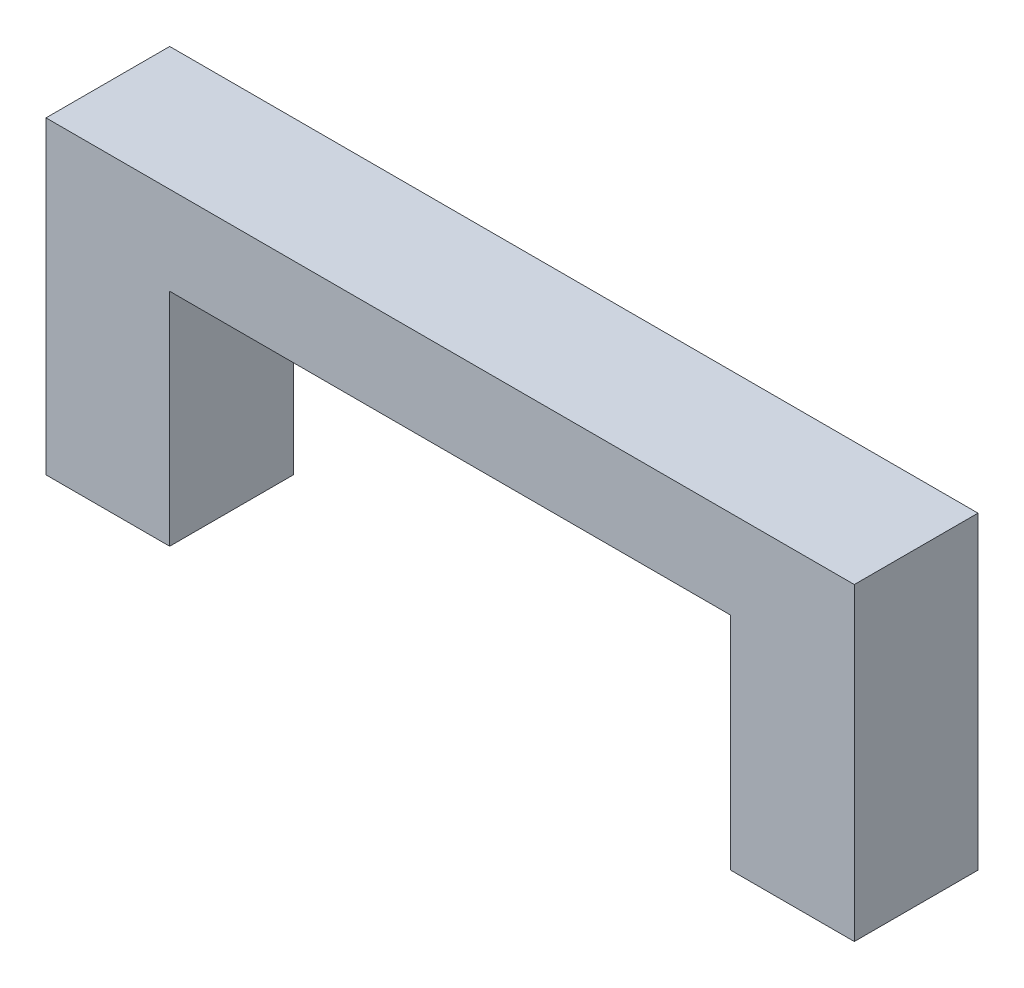
SolidWorks part; units mm, degrees
ref_plane "Front Plane" through (0, 0, 0) normal (0, 0, 1) x (1, 0, 0)
ref_plane "Top Plane" through (0, 0, 0) normal (0, 1, 0) x (1, 0, 0)
ref_plane "Right Plane" through (0, 0, 0) normal (1, 0, 0) x (0, 0, -1)
sketch "Sketch1" plane through (0, 0, 0) normal (0, 0, 1) x (1, 0, 0)
  line L0 (0, 0) -> (0, 7)
  line L1 (0, 7) -> (18.3, 7)
  line L2 (18.3, 7) -> (18.3, 0)
  line L3 (18.3, 0) -> (15.5, 0)
  line L4 (15.5, 0) -> (15.5, 5)
  line L5 (15.5, 5) -> (2.8, 5)
  line L6 (2.8, 5) -> (2.8, 0)
  line L7 (2.8, 0) -> (0, 0)
  point P9 (1.4, 0)
  point P10 (16.9, 0)
  dimension "D1" = 2.8
  dimension "D2" = 5
  dimension "D3" = 7
  dimension "D4" = 15.5
extrude "Boss-Extrude1" add sketch "Sketch1" along normal blind 2.8
sketch "Sketch2" plane through (0, 0, 0) normal (0, -1, 0) x (1, 0, 0)
  line L0 (2.8, 2.8) -> (2.8, 0) construction
  line L1 (0.4, 2.4) -> (2.4, 2.4)
  line L2 (0.4, 2.4) -> (0.4, 0.4)
  line L3 (0.4, 0.4) -> (2.4, 0.4)
  line L4 (2.4, 2.4) -> (2.4, 0.4)
  line L5 (0.4, 2.4) -> (2.4, 0.4) construction
  line L6 (0.4, 0.4) -> (2.4, 2.4) construction
  line L7 (15.9, 2.4) -> (17.9, 2.4)
  line L8 (15.9, 2.4) -> (15.9, 0.4)
  line L9 (15.9, 0.4) -> (17.9, 0.4)
  line L10 (17.9, 2.4) -> (17.9, 0.4)
  line L11 (15.9, 2.4) -> (17.9, 0.4) construction
  line L12 (15.9, 0.4) -> (17.9, 2.4) construction
  line L13 (0, 2.8) -> (2.8, 2.8) construction
  line L14 (18.3, 2.8) -> (18.3, 0) construction
  line L15 (15.5, 2.8) -> (18.3, 2.8) construction
  point P4 (1.4, 1.4)
  point P9 (16.9, 1.4)
  point P12 (2.8, 1.4)
  point P15 (1.4, 2.8)
  point P19 (18.3, 1.4)
  point P23 (16.9, 2.8)
  dimension "D1" = 2
extrude "Cut-Extrude1" cut sketch "Sketch2" against normal blind 2.2 contours L10 L7 L8 L9 | L1 L4 L3 L2
